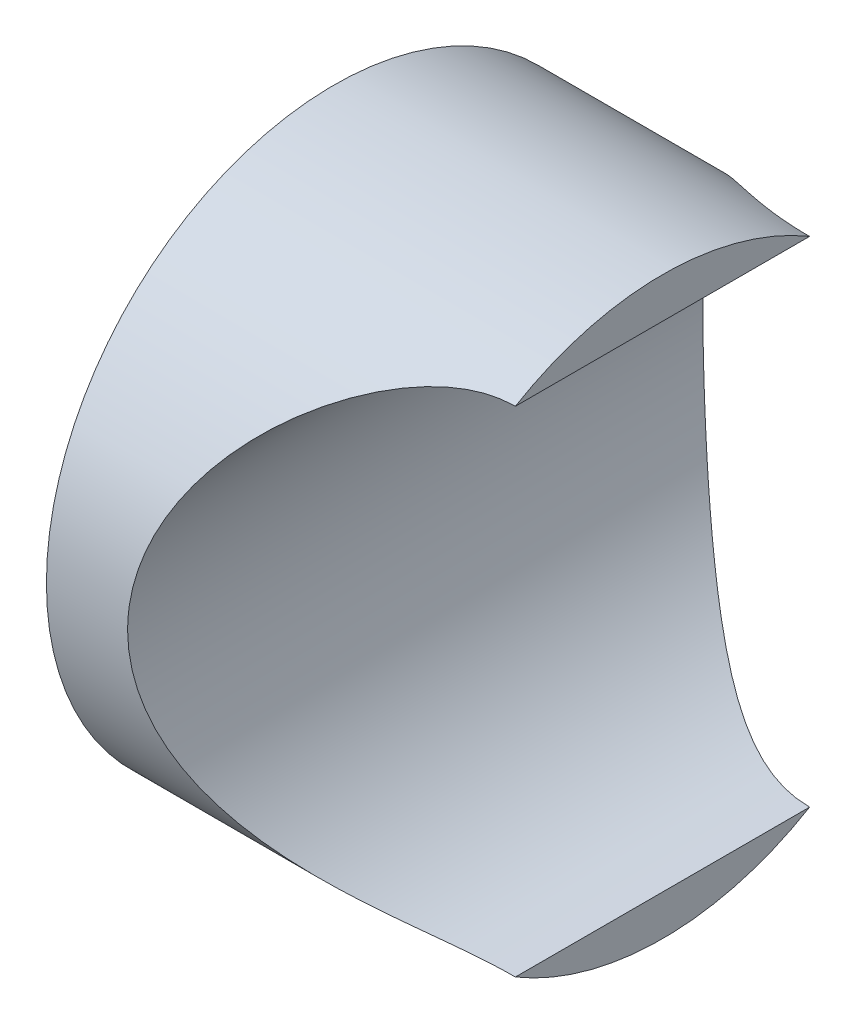
SolidWorks part; units mm, degrees
material "1023 Carbon Steel Sheet (SS)"
ref_plane "Front Plane" through (0, 0, 0) normal (0, 0, 1) x (1, 0, 0)
ref_plane "Top Plane" through (0, 0, 0) normal (0, 1, 0) x (1, 0, 0)
ref_plane "Right Plane" through (0, 0, 0) normal (1, 0, 0) x (0, 0, -1)
sketch "Sketch1" plane through (0, 0, 0) normal (0, 1, 0) x (1, 0, 0)
  line L0 (0, 0) -> (9.8874, 0) construction
  line L1 (12.7815, 13.3831) -> (-2.503, 13.3831)
  line L2 (-2.5061, 13.204) -> (-2.5061, 9.6377)
  line L3 (-2.5061, 9.6377) -> (0, 9.6377)
  line L4 (0, 9.6377) -> (0, 3.705)
  line L6 (12.7808, 11.1256) -> (12.7815, 13.3831)
  line L7 (0, 3.705) -> (0, 0)
  line L8 (0, 0) -> (4.7896, 0)
  line L9 (4.7896, 0) -> (4.8086, 3.705)
  arc A0 (-2.5061, 13.204) -> (-2.503, 13.3831) centre (-3.7472, 13.3151) ccw
  arc A1 (5.1857, 3.559) -> (4.8086, 3.705) centre (4.7896, 3.0959) ccw
  arc A2 (12.4655, 10.7211) -> (5.1857, 3.559) centre (15.8522, -0.0021) ccw
  arc A3 (12.4655, 10.7211) -> (12.7808, 11.1256) centre (10.6602, 12.4531) ccw
revolve "Revolve1" add sketch "Sketch1" angle 360 about L0
ref_plane "Plane3" through (12.7739, 0, 0) normal (-1, 0, 0) x (0, 0, 1)
sketch "Sketch2" plane through (12.7739, 0, 0) normal (-1, 0, 0) x (0, 0, 1)
  line L0 (13.3852, 0) -> (-13.3852, 0)
  line L1 (-16.0778, 11.5) -> (15.5184, 11.5)
  line L2 (15.5184, 11.5) -> (15.5184, 0)
  line L3 (15.5184, 0) -> (13.3852, 0)
  line L5 (-16.0778, 11.5) -> (-16.0778, 0)
  line L6 (-16.0778, 0) -> (-13.3852, 0)
  dimension "D1" = 11.5
  dimension "D2" = 11.5
revolve "Revolved-Cut2" cut sketch "Sketch2" angle 360 about L6
sketch "Sketch5" plane through (0, 0, 0) normal (-1, 0, 0) x (0, 0, 1)
  circle A0 centre (0, 0) radius 5
  dimension "D1" = 10
extrude "Boss-Extrude2" add sketch "Sketch5" along normal blind 2
